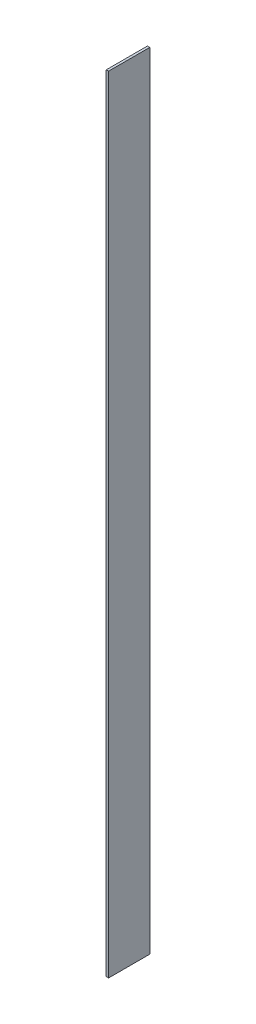
SolidWorks part; units mm, degrees
ref_plane "Front Plane" through (0, 0, 0) normal (0, 0, 1) x (1, 0, 0)
ref_plane "Top Plane" through (0, 0, 0) normal (0, 1, 0) x (1, 0, 0)
ref_plane "Right Plane" through (0, 0, 0) normal (1, 0, 0) x (0, 0, -1)
sketch "Sketch1" plane through (0, 0, 0) normal (1, 0, 0) x (0, 0, -1)
  line L1 (10.5, -200) -> (-10.5, -200)
  line L2 (10.5, -200) -> (10.5, 200)
  line L3 (10.5, 200) -> (-10.5, 200)
  line L4 (-10.5, -200) -> (-10.5, 200)
  line L5 (10.5, -200) -> (-10.5, 200) construction
  line L6 (10.5, 200) -> (-10.5, -200) construction
  point P0 (0, 0)
  dimension "D1" = 21
  dimension "D2" = 400
extrude "Boss-Extrude1" add sketch "Sketch1" along normal mid plane 1.2
